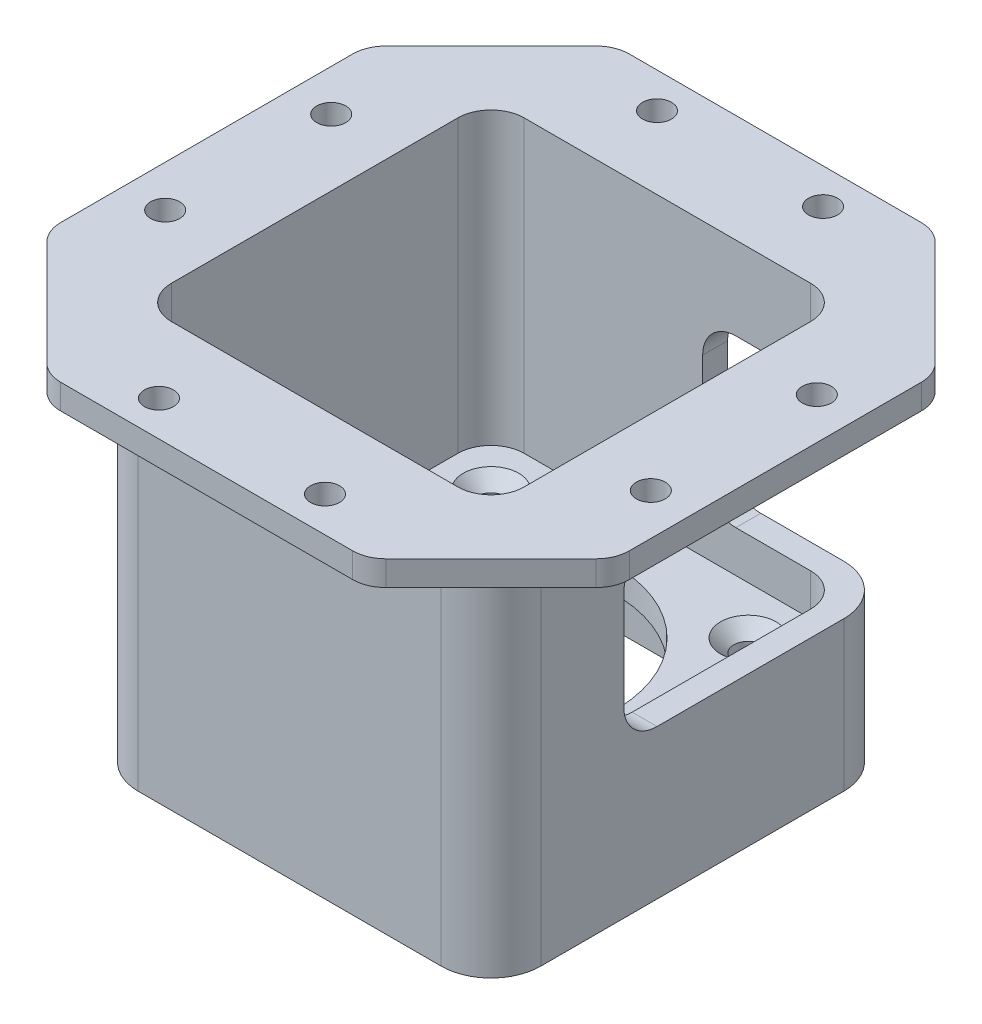
SolidWorks part; units mm, degrees
ref_plane "Front Plane" through (0, 0, 0) normal (0, 0, 1) x (1, 0, 0)
ref_plane "Top Plane" through (0, 0, 0) normal (0, 1, 0) x (1, 0, 0)
ref_plane "Right Plane" through (0, 0, 0) normal (1, 0, 0) x (0, 0, -1)
sketch "Sketch2" plane through (0, 0, 0) normal (0, 1, 0) x (1, 0, 0)
  line L0 (-24.25, 24.25) -> (24.25, 24.25)
  line L1 (-21.25, 21.25) -> (21.25, 21.25) construction
  line L2 (-21.25, 21.25) -> (-21.25, -21.25) construction
  line L3 (-21.25, -21.25) -> (21.25, -21.25) construction
  line L4 (21.25, 21.25) -> (21.25, -21.25) construction
  line L5 (-21.25, 21.25) -> (21.25, -21.25) construction
  line L6 (-21.25, -21.25) -> (21.25, 21.25) construction
  line L7 (24.25, 24.25) -> (24.25, -24.25)
  line L8 (-24.25, -24.25) -> (24.25, -24.25)
  line L9 (-24.25, 24.25) -> (-24.25, -24.25)
  line L10 (-15.5, 15.5) -> (15.5, 15.5) construction
  line L11 (-15.5, 15.5) -> (-15.5, -15.5) construction
  line L12 (-15.5, -15.5) -> (15.5, -15.5) construction
  line L13 (15.5, -15.5) -> (15.5, 15.5) construction
  circle A0 centre (0, 0) radius 15
  circle A1 centre (-15.5, 15.5) radius 1.75
  circle A2 centre (15.5, 15.5) radius 1.75
  circle A3 centre (15.5, -15.5) radius 1.75
  circle A4 centre (-15.5, -15.5) radius 1.75
  point P0 (0, 0)
  dimension "D3" = 30
  dimension "D4" = 3.5
  dimension "D1" = 42.5
  dimension "D2" = 3
  dimension "D5" = 31
extrude "Boss-Extrude1" add sketch "Sketch2" along normal blind 3
sketch "Sketch3" plane through (0, 3, 0) normal (0, 1, 0) x (1, 0, 0)
  line L1 (-21.25, -21.25) -> (21.25, -21.25)
  line L2 (-21.25, -21.25) -> (-21.25, 21.25)
  line L3 (-21.25, 21.25) -> (21.25, 21.25)
  line L4 (21.25, -21.25) -> (21.25, 21.25)
  line L5 (-21.25, -21.25) -> (21.25, 21.25) construction
  line L6 (-21.25, 21.25) -> (21.25, -21.25) construction
  line L7 (-24.25, -24.25) -> (24.25, -24.25)
  line L8 (-24.25, -24.25) -> (-24.25, 24.25)
  line L9 (-24.25, 24.25) -> (24.25, 24.25)
  line L10 (24.25, -24.25) -> (24.25, 24.25)
  line L11 (-24.25, -24.25) -> (24.25, 24.25) construction
  line L12 (-24.25, 24.25) -> (24.25, -24.25) construction
  point P0 (0, 0)
  point P5 (0, 0)
  dimension "D1" = 42.5
extrude "Boss-Extrude2" add sketch "Sketch3" along normal blind 32
sketch "Sketch4" plane through (0, 35, 0) normal (0, 1, 0) x (1, 0, 0)
  line L1 (-21.25, -21.25) -> (21.25, -21.25)
  line L2 (-21.25, -21.25) -> (-21.25, 21.25)
  line L3 (-21.25, 21.25) -> (21.25, 21.25)
  line L4 (21.25, -21.25) -> (21.25, 21.25)
  line L5 (-21.25, -21.25) -> (21.25, 21.25) construction
  line L6 (-21.25, 21.25) -> (21.25, -21.25) construction
  line L23 (-34.25, 0) -> (34.25, 0) construction
  line L24 (-34.25, 10) -> (34.25, 10) construction
  line L44 (-34.25, -10) -> (34.25, -10) construction
  line L45 (0, -34.25) -> (0, 34.25) construction
  line L46 (34.25, -34.25) -> (34.25, 34.25)
  line L47 (34.25, 34.25) -> (-34.25, 34.25)
  line L48 (-34.25, 34.25) -> (-34.25, -34.25)
  line L49 (-34.25, -34.25) -> (34.25, -34.25)
  line L50 (34.25, -34.25) -> (34.25, 34.25)
  line L51 (34.25, 34.25) -> (-34.25, 34.25)
  line L52 (-34.25, 34.25) -> (-34.25, -34.25)
  line L53 (-34.25, -34.25) -> (34.25, -34.25)
  line L54 (-10, 34.25) -> (-10, -34.25) construction
  line L55 (10, 34.25) -> (10, -34.25) construction
  line L56 (-34.25, 30) -> (34.25, 30) construction
  line L57 (-29.25, 10) -> (-29.25, -10) construction
  line L58 (29.25, 10) -> (29.25, -10) construction
  line L59 (-34.25, -30) -> (34.25, -30) construction
  circle A0 centre (-10, 30) radius 1.75
  circle A1 centre (10, 30) radius 1.75
  circle A2 centre (-29.25, 10) radius 1.75
  circle A3 centre (-29.25, -10) radius 1.75
  circle A4 centre (-10, -30) radius 1.75
  circle A5 centre (10, -30) radius 1.75
  circle A6 centre (29.25, -10) radius 1.75
  circle A7 centre (29.25, 10) radius 1.75
  point P0 (0, 0)
  dimension "D6" = 3.5
  dimension "D7" = 3.5
  dimension "D9" = 3.5
  dimension "D1" = 10
  dimension "D2" = 10
  dimension "D3" = 10
  dimension "D4" = 10
  dimension "D5" = 10
  dimension "D8" = 20
  dimension "D10" = 20
  dimension "D11" = 5
  dimension "D12" = 5
extrude "Boss-Extrude3" add sketch "Sketch4" along normal blind 3
chamfer "Chamfer1" distance 15 angle 45 4 edges at (34.25, 36.5, 34.25) (34.25, 36.5, -34.25) (-34.25, 36.5, -34.25) (-34.25, 36.5, 34.25)
sketch "Sketch5" plane through (0, 0, 0) normal (0, -1, 0) x (1, 0, 0)
  line L1 (-21.25, 21.25) -> (21.25, 21.25)
  line L2 (-21.25, 21.25) -> (-21.25, -21.25)
  line L3 (-21.25, -21.25) -> (21.25, -21.25)
  line L4 (21.25, 21.25) -> (21.25, -21.25)
  line L5 (-21.25, 21.25) -> (21.25, -21.25) construction
  line L6 (-21.25, -21.25) -> (21.25, 21.25) construction
  line L7 (-24.25, -24.25) -> (24.25, -24.25)
  line L8 (-24.25, -24.25) -> (-24.25, 24.25)
  line L9 (-24.25, 24.25) -> (24.25, 24.25)
  line L10 (24.25, -24.25) -> (24.25, 24.25)
  line L11 (-24.25, -24.25) -> (24.25, 24.25) construction
  line L12 (-24.25, 24.25) -> (24.25, -24.25) construction
  line L13 (24.25, -24.25) -> (-24.25, -24.25) construction
  point P0 (0, 0)
  point P5 (0, 0)
  dimension "D1" = 42.5
extrude "Boss-Extrude4" add sketch "Sketch5" along normal blind 10
fillet "Fillet1" radius 6 4 edges at (-24.25, 12.5, 24.25) (-24.25, 12.5, -24.25) (24.25, 12.5, 24.25) (24.25, 12.5, -24.25)
sketch "Sketch7" plane through (24.25, 0, 0) normal (1, 0, 0) x (0, 0, -1)
  line L0 (21.25, 0) -> (-21.25, 0) construction
  line L1 (-8.25, 28) -> (36.75, 28)
  line L2 (-8.25, 28) -> (-8.25, 8)
  line L3 (-8.25, 8) -> (36.75, 8)
  line L4 (36.75, 28) -> (36.75, 8)
  line L5 (-18.25, 35) -> (-18.25, -10) construction
  dimension "D1" = 20
  dimension "D2" = 45
  dimension "D3" = 28
  dimension "D4" = 10
extrude "Cut-Extrude2" cut sketch "Sketch7" against normal blind 20
fillet "Fillet2" radius 4 8 edges at (-19.25, 36.5, 34.25) (-34.25, 36.5, 19.25) (-34.25, 36.5, -19.25) (-19.25, 36.5, -34.25) (19.25, 36.5, -34.25) (34.25, 36.5, -19.25) (19.25, 36.5, 34.25) (34.25, 36.5, 19.25)
chamfer "Chamfer2" distance 1.6 angle 45 4 edges at (-15.5, 3, 17.25) (-15.5, 3, -13.75) (15.5, 3, 17.25) (15.5, 3, -13.75)
fillet "Fillet4" radius 4 5 edges at (-21.25, 20.5, -21.25) (-21.25, 20.5, 21.25) (21.25, 20.5, 21.25) (21.25, 5.5, -21.25) (21.25, 33, -21.25)
fillet "Fillet5" radius 4 4 edges at (22.75, 28, 8.25) (22.75, 8, 8.25) (4.25, 28, -22.75) (4.25, 8, -22.75)
fillet "Fillet6" radius 3 4 edges at (-21.25, -5, -21.25) (-21.25, -5, 21.25) (21.25, -5, -21.25) (21.25, -5, 21.25)
